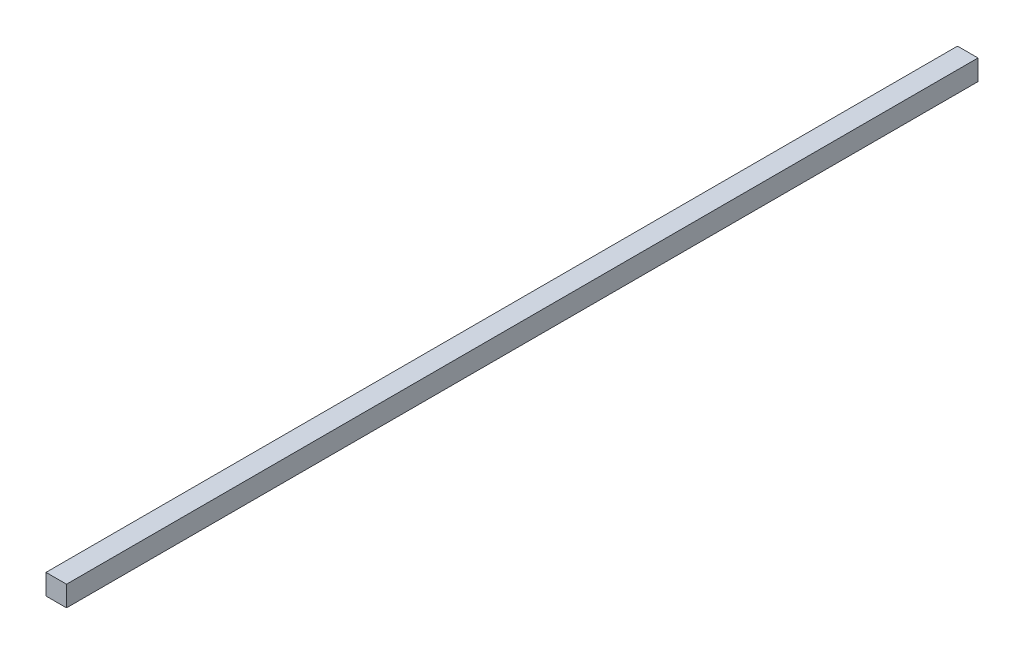
SolidWorks part; units mm, degrees
ref_plane "Front Plane" through (0, 0, 0) normal (0, 0, 1) x (1, 0, 0)
ref_plane "Top Plane" through (0, 0, 0) normal (0, 1, 0) x (1, 0, 0)
ref_plane "Right Plane" through (0, 0, 0) normal (1, 0, 0) x (0, 0, -1)
sketch "Sketch1" plane through (0, 0, 0) normal (0, 0, 1) x (1, 0, 0)
  line L1 (0, 0) -> (45, 0)
  line L2 (0, 0) -> (0, 45)
  line L3 (0, 45) -> (45, 45)
  line L4 (45, 0) -> (45, 45)
  dimension "D1" = 45
  dimension "D2" = 45
extrude "Boss-Extrude1" add sketch "Sketch1" along normal blind 2000
